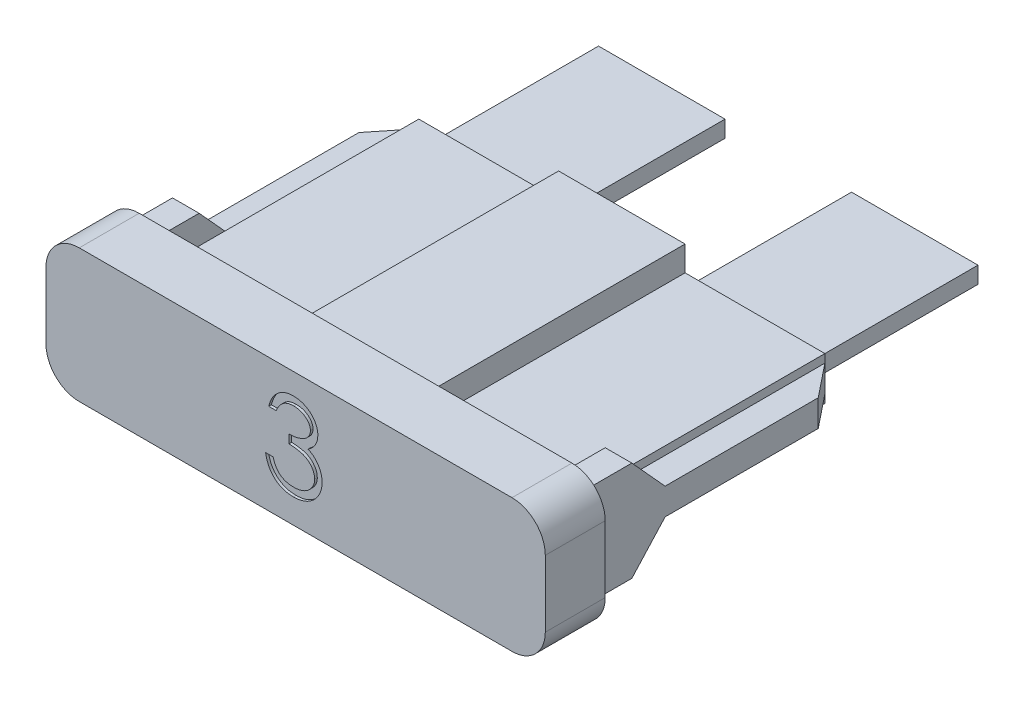
SolidWorks part; units mm, degrees
ref_plane "Front Plane" through (0, 0, 0) normal (0, 0, 1) x (1, 0, 0)
ref_plane "Top Plane" through (0, 0, 0) normal (0, 1, 0) x (1, 0, 0)
ref_plane "Right Plane" through (0, 0, 0) normal (1, 0, 0) x (0, 0, -1)
sketch "Sketch1" plane through (0, 0, 0) normal (0, 0, 1) x (1, 0, 0)
  line L1 (1.27, 0) -> (17.78, 0)
  line L2 (0, 1.27) -> (0, 3.81)
  line L3 (1.27, 5.08) -> (17.78, 5.08)
  line L4 (19.05, 1.27) -> (19.05, 3.81)
  arc A0 (0, 3.81) -> (1.27, 5.08) centre (1.27, 3.81) cw
  arc A1 (1.27, 0) -> (0, 1.27) centre (1.27, 1.27) cw
  arc A2 (19.05, 1.27) -> (17.78, 0) centre (17.78, 1.27) cw
  arc A3 (17.78, 5.08) -> (19.05, 3.81) centre (17.78, 3.81) cw
  point P8 (0, 0)
  dimension "D3" = 1.27
  dimension "D1" = 5.08
  dimension "D2" = 19.05
extrude "Extrude1" add sketch "Sketch1" along normal blind 2.286
sketch "Sketch2" plane through (0, 0, 0) normal (0, 0, -1) x (-1, 0, 0)
  line L0 (-7.62, 2.2225) -> (-7.62, 1.27)
  line L1 (-16.764, 2.8575) -> (-11.43, 2.8575)
  line L2 (-16.764, 2.8575) -> (-16.764, 2.2225)
  line L3 (-16.764, 2.2225) -> (-11.43, 2.2225)
  line L4 (-11.43, 2.2225) -> (-11.43, 1.27)
  line L5 (-11.43, 3.81) -> (-7.62, 3.81)
  line L6 (-11.43, 3.81) -> (-11.43, 2.8575)
  line L7 (-11.43, 1.27) -> (-7.62, 1.27)
  line L8 (-7.62, 3.81) -> (-7.62, 2.8575)
  line L9 (-7.62, 2.8575) -> (-2.286, 2.8575)
  line L10 (-11.938, 4.318) -> (-11.938, 3.3655)
  line L11 (-7.62, 2.2225) -> (-2.286, 2.2225)
  line L12 (-2.286, 2.8575) -> (-2.286, 2.2225)
  line L13 (-17.272, 3.3655) -> (-11.938, 3.3655)
  line L14 (-17.272, 3.3655) -> (-17.272, 1.7145)
  line L15 (-17.272, 1.7145) -> (-11.938, 1.7145)
  line L16 (-11.938, 1.7145) -> (-11.938, 0.762)
  line L17 (-11.938, 0.762) -> (-7.112, 0.762)
  line L18 (-7.112, 1.7145) -> (-7.112, 0.762)
  line L19 (-7.112, 1.7145) -> (-1.778, 1.7145)
  line L20 (-1.778, 3.3655) -> (-1.778, 1.7145)
  line L21 (-7.112, 3.3655) -> (-1.778, 3.3655)
  line L22 (-7.112, 4.318) -> (-7.112, 3.3655)
  line L23 (-11.938, 4.318) -> (-7.112, 4.318)
  line L24 (-17.78, 5.08) -> (-1.27, 5.08) construction
  line L25 (-1.27, 0) -> (-17.78, 0) construction
  line L26 (-19.05, 1.27) -> (-19.05, 3.81) construction
  line L27 (0, 3.81) -> (0, 1.27) construction
  dimension "D1" = 0.635
  dimension "D2" = 2.54
  dimension "D3" = 0.9525
  dimension "D5" = 0.762
  dimension "D6" = 0.762
  dimension "D7" = 1.778
  dimension "D8" = 14.478
  dimension "D9" = 3.81
  dimension "D10" = 5.334
  dimension "D11" = 5.334
  dimension "D12" = 1.778
  dimension "D4" = 0.508
extrude "Extrude2" add sketch "Sketch2" along normal blind 10.16
sketch "Sketch3" plane through (1.778, 0, 0) normal (-1, 0, 0) x (0, 0, 1)
  line L0 (-10.16, 1.7145) -> (-10.16, 3.3655) construction
  line L1 (-10.16, 3.048) -> (-3.048, 3.048)
  line L2 (-10.16, 3.048) -> (-10.16, 2.032)
  line L3 (-10.16, 2.032) -> (-3.048, 2.032)
  line L5 (0, 3.81) -> (0, 1.27) construction
  line L6 (-1.778, 4.445) -> (0, 4.445)
  line L8 (-1.778, 0.635) -> (0, 0.635)
  line L9 (0, 4.445) -> (0, 0.635)
  line L10 (-10.16, 3.3655) -> (0, 3.3655) construction
  line L11 (-10.16, 1.7145) -> (0, 1.7145) construction
  line L12 (-1.778, 4.445) -> (-3.048, 3.048)
  line L13 (-3.048, 2.032) -> (-1.778, 0.635)
  dimension "D1" = 1.016
  dimension "D2" = 0.3175
  dimension "D3" = 0.3175
  dimension "D4" = 3.81
  dimension "D5" = 1.397
  dimension "D6" = 1.397
  dimension "D7" = 1.27
  dimension "D8" = 1.778
extrude "Extrude3" add sketch "Sketch3" along normal blind 1.016
sketch "Sketch4" plane through (17.272, 0, 0) normal (1, 0, 0) x (0, 0, -1)
  line L0 (10.16, 3.3655) -> (10.16, 1.7145) construction
  line L1 (3.048, 3.048) -> (10.16, 3.048)
  line L3 (3.048, 2.032) -> (10.16, 2.032)
  line L4 (10.16, 3.048) -> (10.16, 2.032)
  line L5 (0, 3.81) -> (0, 5.08) construction
  line L6 (0, 4.445) -> (1.778, 4.445)
  line L7 (0, 4.445) -> (0, 0.635)
  line L8 (0, 0.635) -> (1.778, 0.635)
  line L10 (1.778, 4.445) -> (3.048, 3.048)
  line L11 (1.778, 0.635) -> (3.048, 2.032)
  line L12 (10.16, 3.3655) -> (0, 3.3655) construction
  dimension "D1" = 1.016
  dimension "D2" = 0.3175
  dimension "D3" = 1.397
  dimension "D4" = 3.81
  dimension "D5" = 1.27
  dimension "D6" = 7.112
extrude "Extrude4" add sketch "Sketch4" along normal blind 1.016
chamfer "Chamfer1" distance 1.016 distance2 1.27 2 edges at (0.762, 2.54, -10.16) (18.288, 2.54, -10.16)
sketch "Sketch8" plane through (0, 2.2225, 0) normal (0, 1, 0) x (-1, 0, 0)
  line L0 (-11.938, -10.16) -> (-11.938, 0) construction
  line L1 (-2.286, 0) -> (-7.112, 0)
  line L2 (-2.286, 0) -> (-2.286, -16.51)
  line L3 (-2.286, -16.51) -> (-7.112, -16.51)
  line L4 (-7.112, 0) -> (-7.112, -6.858)
  line L5 (-16.764, 0) -> (-11.938, 0)
  line L6 (-16.764, 0) -> (-16.764, -16.51)
  line L7 (-16.764, -16.51) -> (-11.938, -16.51)
  line L8 (-11.938, 0) -> (-11.938, -6.858)
  line L9 (-7.112, -10.16) -> (-7.112, 0) construction
  line L10 (-1.778, -10.16) -> (-7.112, -10.16) construction
  line L11 (-11.938, -10.16) -> (-17.272, -10.16) construction
  line L12 (-7.112, -7.62) -> (-8.128, -7.62)
  line L13 (-8.763, -6.985) -> (-8.763, -3.175)
  line L14 (-9.398, -2.54) -> (-9.652, -2.54)
  line L15 (-10.287, -3.175) -> (-10.287, -6.985)
  line L16 (-10.922, -7.62) -> (-11.938, -7.62)
  line L17 (-7.112, -10.16) -> (-11.938, -10.16) construction
  line L18 (-11.684, -6.858) -> (-11.938, -6.858)
  line L19 (-11.049, -3.175) -> (-11.049, -6.223)
  line L20 (-9.398, -1.778) -> (-9.652, -1.778)
  line L21 (-8.001, -6.223) -> (-8.001, -3.175)
  line L22 (-7.112, -6.858) -> (-7.366, -6.858)
  line L23 (-11.938, -7.62) -> (-11.938, -16.51)
  line L24 (-7.112, -7.62) -> (-7.112, -16.51)
  arc A0 (-9.652, -2.54) -> (-10.287, -3.175) centre (-9.652, -3.175) ccw
  arc A1 (-8.763, -3.175) -> (-9.398, -2.54) centre (-9.398, -3.175) ccw
  arc A2 (-10.922, -7.62) -> (-10.287, -6.985) centre (-10.922, -6.985) ccw
  arc A3 (-8.128, -7.62) -> (-8.763, -6.985) centre (-8.128, -6.985) cw
  arc A4 (-9.652, -1.778) -> (-11.049, -3.175) centre (-9.652, -3.175) ccw
  arc A5 (-8.001, -3.175) -> (-9.398, -1.778) centre (-9.398, -3.175) ccw
  arc A6 (-7.366, -6.858) -> (-8.001, -6.223) centre (-7.366, -6.223) cw
  arc A7 (-11.684, -6.858) -> (-11.049, -6.223) centre (-11.684, -6.223) ccw
  point P26 (-10.287, -2.54)
  point P29 (-8.763, -2.54)
  point P32 (-10.287, -7.62)
  point P35 (-8.763, -7.62)
  dimension "D6" = 0.635
  dimension "D8" = 0.635
  dimension "D1" = 6.35
  dimension "D2" = 6.35
  dimension "D3" = 1.524
  dimension "D4" = 5.08
  dimension "D5" = 2.54
  dimension "D7" = 0.762
extrude "Blade" add sketch "Sketch8" along normal up to surface (0.635 mm away) up to face at (4.953, 2.8575, -5.08)
sketch "Sketch5" plane through (0, 0, 2.286) normal (0, 0, 1) x (1, 0, 0)
  line L0 (0, 3.81) -> (0, 1.27) construction
  line L1 (1.27, 0) -> (17.78, 0) construction
  text T0 "10" font "Century Gothic" height in points 12
  dimension "D1" = 6.7818
  dimension "D2" = 0.9525
extrude "\"10\"" [suppressed] cut sketch "Sketch5" against normal blind 0.1016
sketch "Sketch6" [suppressed] plane through (0, 0, 2.286) normal (0, 0, 1) x (1, 0, 0)
  line L0 (1.27, 0) -> (17.78, 0) construction
  line L1 (0, 3.81) -> (0, 1.27) construction
  text T0 "40" font "Century Gothic" height in points 12
  dimension "D1" = 1.016
  dimension "D2" = 6.985
extrude "\"40\"" [suppressed] cut sketch "Sketch6" against normal blind 0.1016
sketch "Sketch7" [suppressed] plane through (0, 0, 2.286) normal (0, 0, 1) x (1, 0, 0)
  line L0 (1.27, 0) -> (17.78, 0) construction
  line L1 (0, 3.81) -> (0, 1.27) construction
  text T0 "30" font "Century Gothic" height in points 12
  dimension "D1" = 1.016
  dimension "D2" = 6.985
extrude "\"30\"" [suppressed] cut sketch "Sketch7" against normal blind 0.1016
sketch "Sketch9" [suppressed] plane through (0, 0, 2.286) normal (0, 0, 1) x (1, 0, 0)
  line L0 (1.27, 0) -> (17.78, 0) construction
  line L1 (0, 3.81) -> (0, 1.27) construction
  text T0 "7.5" font "Century Gothic" height in points 12
  dimension "D1" = 1.016
  dimension "D2" = 6.604
extrude "\"7.5\"" [suppressed] cut sketch "Sketch9" against normal blind 0.1016
sketch "Sketch10" [suppressed] plane through (0, 0, 2.286) normal (0, 0, 1) x (1, 0, 0)
  line L0 (1.27, 0) -> (17.78, 0) construction
  line L1 (0, 3.81) -> (0, 1.27) construction
  text T0 "1" font "Century Gothic" height in points 12
  dimension "D1" = 1.016
  dimension "D2" = 8.255
extrude "\"1\"" [suppressed] cut sketch "Sketch10" against normal blind 0.1016
sketch "Sketch11" [suppressed] plane through (0, 0, 2.286) normal (0, 0, 1) x (1, 0, 0)
  line L0 (1.27, 0) -> (17.78, 0) construction
  line L1 (0, 3.81) -> (0, 1.27) construction
  text T0 "15" font "Century Gothic" height in points 12
  dimension "D1" = 1.016
  dimension "D2" = 6.858
extrude "\"15\"" [suppressed] cut sketch "Sketch11" against normal blind 0.1016
sketch "Sketch12" [suppressed] plane through (0, 0, 2.286) normal (0, 0, 1) x (1, 0, 0)
  line L0 (1.27, 0) -> (17.78, 0) construction
  line L1 (0, 3.81) -> (0, 1.27) construction
  text T0 "2" font "Century Gothic" height in points 12
  dimension "D1" = 1.016
  dimension "D2" = 8.255
extrude "\"2\"" [suppressed] cut sketch "Sketch12" against normal blind 0.1016
sketch "Sketch13" [suppressed] plane through (0, 0, 2.286) normal (0, 0, 1) x (1, 0, 0)
  line L0 (1.27, 0) -> (17.78, 0) construction
  line L1 (0, 3.81) -> (0, 1.27) construction
  text T0 "20" font "Century Gothic" height in points 12
  dimension "D1" = 1.016
  dimension "D2" = 6.985
extrude "\"20\"" [suppressed] cut sketch "Sketch13" against normal blind 0.1016
sketch "Sketch14" [suppressed] plane through (0, 0, 2.286) normal (0, 0, 1) x (1, 0, 0)
  line L0 (1.27, 0) -> (17.78, 0) construction
  line L1 (0, 3.81) -> (0, 1.27) construction
  text T0 "25" font "Century Gothic" height in points 12
  dimension "D1" = 1.016
  dimension "D2" = 6.985
extrude "\"25\"" [suppressed] cut sketch "Sketch14" against normal blind 0.1016
sketch "Sketch15" plane through (0, 0, 2.286) normal (0, 0, 1) x (1, 0, 0)
  line L0 (1.27, 0) -> (17.78, 0) construction
  line L1 (0, 3.81) -> (0, 1.27) construction
  text T0 "3" font "Century Gothic" height in points 12
  dimension "D1" = 1.016
  dimension "D2" = 8.255
extrude "\"3\"" cut sketch "Sketch15" against normal blind 0.1016
sketch "Sketch16" [suppressed] plane through (0, 0, 2.286) normal (0, 0, 1) x (1, 0, 0)
  line L0 (1.27, 0) -> (17.78, 0) construction
  line L1 (0, 3.81) -> (0, 1.27) construction
  text T0 "4" font "Century Gothic" height in points 12
  dimension "D1" = 1.016
  dimension "D2" = 8.255
extrude "\"4\"" [suppressed] cut sketch "Sketch16" against normal blind 0.1016
sketch "Sketch17" [suppressed] plane through (0, 0, 2.286) normal (0, 0, 1) x (1, 0, 0)
  line L0 (1.27, 0) -> (17.78, 0) construction
  line L1 (0, 3.81) -> (0, 1.27) construction
  text T0 "5" font "Century Gothic" height in points 12
  dimension "D1" = 1.016
  dimension "D2" = 8.255
extrude "\"5\"" [suppressed] cut sketch "Sketch17" against normal blind 0.1016
sketch3d "3DSketch1" [suppressed]
  line L0 (1.27, 0, 2.286) -> (17.78, 0, 2.286) construction
  point P0 (9.525, 0, 2.286)
ref_plane "Plane1" [suppressed] through (9.525, 0, 0) normal (1, 0, 0) x (0, 0, -1)
sketch3d "3DSketch2" [suppressed]
  line L0 (16.764, 2.8575, -16.51) -> (11.938, 2.2225, -16.51) construction
  line L1 (7.112, 2.8575, -16.51) -> (2.286, 2.2225, -16.51) construction
  line L2 (4.699, 2.54, -16.51) -> (4.699, 2.54, -10.3726) construction
  line L3 (14.351, 2.54, -16.51) -> (14.351, 2.54, -10.2814) construction
